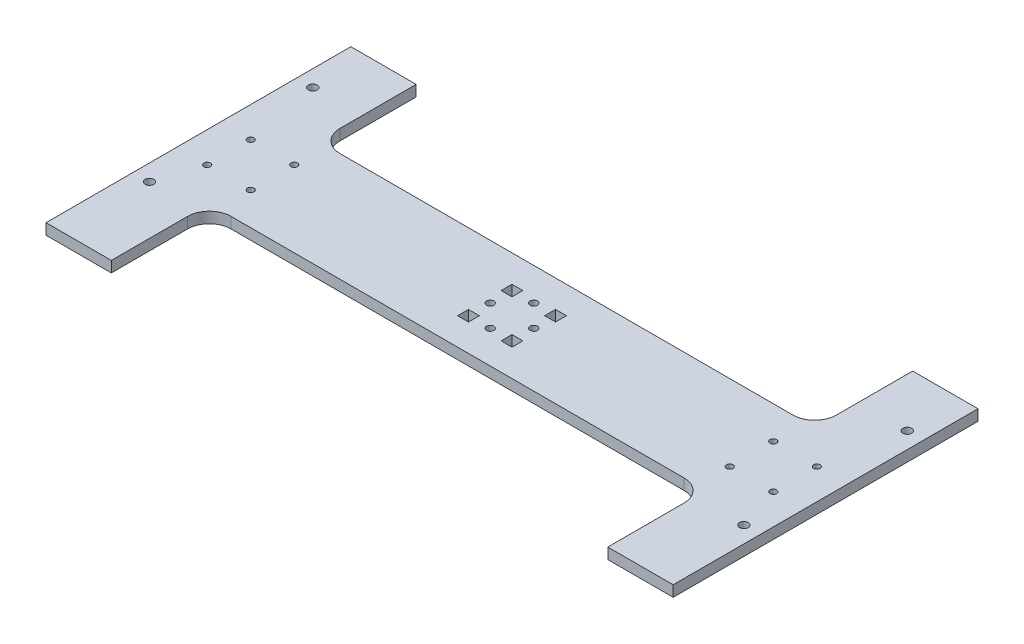
SolidWorks part; units mm, degrees
ref_plane "Front Plane" through (0, 0, 0) normal (0, 0, 1) x (1, 0, 0)
ref_plane "Top Plane" through (0, 0, 0) normal (0, 1, 0) x (1, 0, 0)
ref_plane "Right Plane" through (0, 0, 0) normal (1, 0, 0) x (0, 0, -1)
sketch "Sketch1" plane through (0, 0, 0) normal (0, 1, 0) x (1, 0, 0)
  line L1 (144, -25) -> (-144, -25)
  line L2 (144, -25) -> (144, 25)
  line L3 (144, 25) -> (-144, 25)
  line L4 (-144, -25) -> (-144, 25)
  line L5 (144, -25) -> (-144, 25) construction
  line L6 (144, 25) -> (-144, -25) construction
  point P0 (0, 0)
  dimension "D1" = 50
  dimension "D2" = 288
extrude "Boss-Extrude1" add sketch "Sketch1" along normal blind 5
sketch "Sketch2" plane through (0, 5, 0) normal (0, 1, 0) x (1, 0, 0)
  line L0 (-144, 25) -> (-144, -25) construction
  line L1 (-2.75, 0) -> (2.75, 0) construction
  line L2 (0, -2.75) -> (0, 2.75) construction
  circle A0 centre (-130, 10) radius 1.5
  circle A1 centre (-110, 10) radius 1.5
  circle A2 centre (-110, -10) radius 1.5
  circle A3 centre (-130, -10) radius 1.5
  circle A4 centre (130, -10) radius 1.5
  circle A5 centre (110, -10) radius 1.5
  circle A6 centre (110, 10) radius 1.5
  circle A7 centre (130, 10) radius 1.5
  point P6 (-144, 0)
  dimension "D1" = 20
  dimension "D2" = 10
  dimension "D3" = 14
extrude "Cut-Extrude1" cut sketch "Sketch2" against normal blind 5
sketch "Sketch3" plane through (0, 5, 0) normal (0, 1, 0) x (1, 0, 0)
  line L0 (-2.75, 0) -> (2.75, 0) construction
  line L1 (-144, 25) -> (-114, 25)
  line L2 (-144, 25) -> (-144, 70)
  line L3 (-144, 70) -> (-114, 70)
  line L4 (-114, 25) -> (-114, 70)
  line L5 (-114, -25) -> (-114, -70)
  line L6 (-144, -70) -> (-114, -70)
  line L7 (-144, -25) -> (-144, -70)
  line L8 (-144, -25) -> (-114, -25)
  line L9 (0, -2.75) -> (0, 2.75) construction
  line L10 (144, -25) -> (114, -25)
  line L11 (144, -25) -> (144, -70)
  line L12 (144, -70) -> (114, -70)
  line L13 (114, -25) -> (114, -70)
  line L14 (114, 25) -> (114, 70)
  line L15 (144, 70) -> (114, 70)
  line L16 (144, 25) -> (144, 70)
  line L17 (144, 25) -> (114, 25)
  dimension "D1" = 30
  dimension "D2" = 45
extrude "Boss-Extrude2" add sketch "Sketch3" against normal blind 5
fillet "Fillet1" radius 10 4 edges at (114, 2.5, 25) (114, 2.5, -25) (-114, 2.5, 25) (-114, 2.5, -25)
sketch "Sketch4" plane through (0, 5, 0) normal (0, 1, 0) x (1, 0, 0)
  line L0 (0, -2.75) -> (0, 2.75) construction
  line L1 (12.5, 7.5) -> (7.5, 7.5)
  line L2 (12.5, 7.5) -> (12.5, 12.5)
  line L3 (12.5, 12.5) -> (7.5, 12.5)
  line L4 (7.5, 7.5) -> (7.5, 12.5)
  line L5 (12.5, 7.5) -> (7.5, 12.5) construction
  line L6 (12.5, 12.5) -> (7.5, 7.5) construction
  line L7 (-12.5, 12.5) -> (-7.5, 7.5) construction
  line L8 (-12.5, 7.5) -> (-7.5, 12.5) construction
  line L9 (-7.5, 7.5) -> (-7.5, 12.5)
  line L10 (-12.5, 12.5) -> (-7.5, 12.5)
  line L11 (-12.5, 7.5) -> (-12.5, 12.5)
  line L12 (-12.5, 7.5) -> (-7.5, 7.5)
  line L13 (-2.75, 0) -> (2.75, 0) construction
  line L14 (-12.5, -7.5) -> (-7.5, -12.5) construction
  line L15 (-12.5, -12.5) -> (-7.5, -7.5) construction
  line L16 (12.5, -12.5) -> (7.5, -7.5) construction
  line L17 (12.5, -7.5) -> (7.5, -12.5) construction
  line L18 (-12.5, -7.5) -> (-7.5, -7.5)
  line L19 (-12.5, -7.5) -> (-12.5, -12.5)
  line L20 (-12.5, -12.5) -> (-7.5, -12.5)
  line L21 (-7.5, -7.5) -> (-7.5, -12.5)
  line L22 (7.5, -7.5) -> (7.5, -12.5)
  line L23 (12.5, -12.5) -> (7.5, -12.5)
  line L24 (12.5, -7.5) -> (12.5, -12.5)
  line L25 (12.5, -7.5) -> (7.5, -7.5)
  point P0 (10, 10)
  point P12 (-10, 10)
  point P23 (-10, -10)
  point P24 (10, -10)
  dimension "D1" = 5
  dimension "D2" = 5
  dimension "D3" = 10
  dimension "D4" = 10
extrude "Cut-Extrude2" cut sketch "Sketch4" against normal blind 5
sketch "Sketch5" plane through (0, 5, 0) normal (0, 1, 0) x (1, 0, 0)
  circle A0 centre (0, 10) radius 1.7
  circle A1 centre (0, -10) radius 1.7
  circle A2 centre (10, 0) radius 1.7
  circle A3 centre (-10, 0) radius 1.7
extrude "Cut-Extrude3" cut sketch "Sketch5" against normal blind 5
sketch "Sketch7" plane through (0, 5, 0) normal (0, 1, 0) x (1, 0, 0)
  line L0 (0, -2.75) -> (0, 2.75) construction
  circle A0 centre (-136.5, 45) radius 2
  circle A1 centre (-136.5, -30) radius 2
  circle A2 centre (136.5, -30) radius 2
  circle A3 centre (136.5, 45) radius 2
extrude "Cut-Extrude4" cut sketch "Sketch7" against normal blind 10
